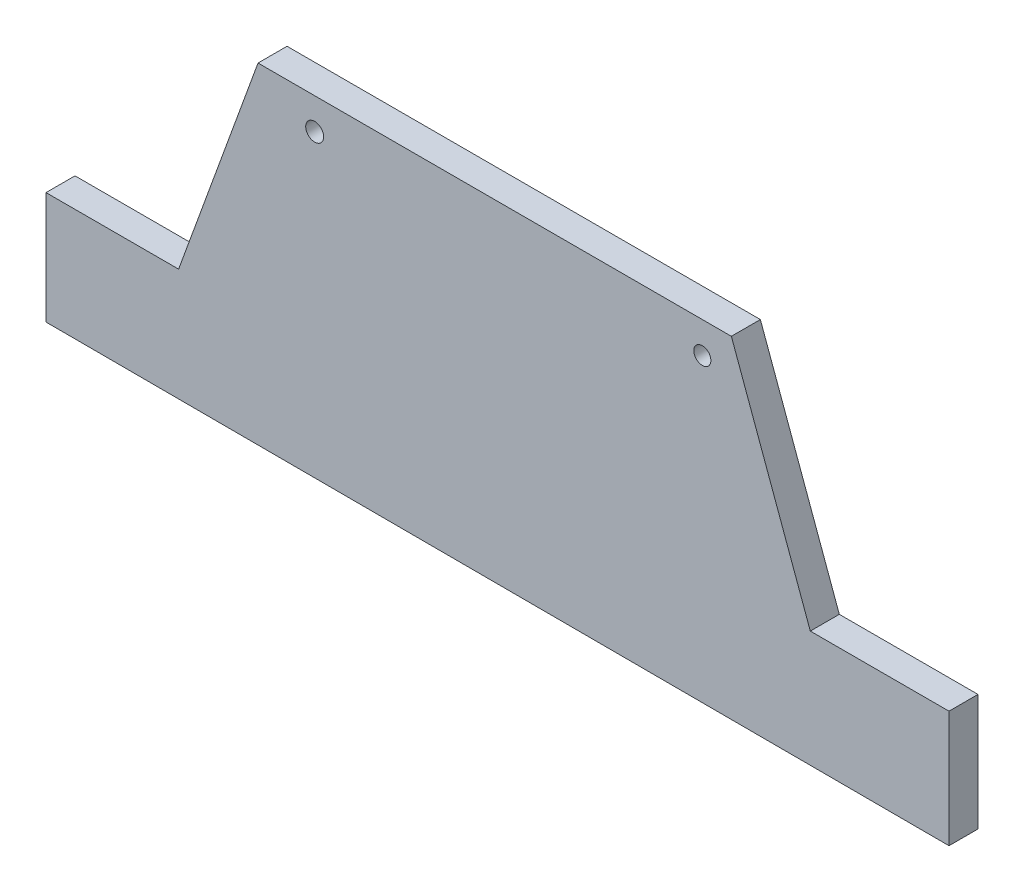
SolidWorks part; units mm, degrees
ref_plane "Front Plane" through (0, 0, 0) normal (0, 0, 1) x (1, 0, 0)
ref_plane "Top Plane" through (0, 0, 0) normal (0, 1, 0) x (1, 0, 0)
ref_plane "Right Plane" through (0, 0, 0) normal (1, 0, 0) x (0, 0, -1)
sketch "Sketch1" plane through (0, 0, 0) normal (0, 0, 1) x (1, 0, 0)
  line L0 (-49.7678, -29.9114) -> (123.0668, -29.9114)
  line L1 (-169.5558, 0) -> (-169.5558, 50)
  line L2 (233.0442, -0.8952) -> (233.0442, 51.0695)
  line L3 (233.0442, 51.0695) -> (171.2122, 51.0695)
  line L4 (-169.5558, 50) -> (-110.432, 50)
  line L5 (-110.432, 50) -> (-75.018, 147.2991)
  line L6 (171.2122, 51.0695) -> (136.0126, 147.2991)
  line L7 (-169.5558, 0) -> (233.0442, -0.8952)
  line L8 (136.0126, 147.2991) -> (-75.018, 147.2991)
  line L13 (67.0636, 0) -> (-67.0636, 0) construction
  circle A0 centre (-49.7678, 133.3926) radius 4
  circle A1 centre (123.0668, 133.3926) radius 3.8175
extrude "Boss-Extrude1" add sketch "Sketch1" along normal blind 12.9338 and the other way blind 0.0001 contours L6 L8 L5 L4 L1 L7 L2 L3 A1 A0
